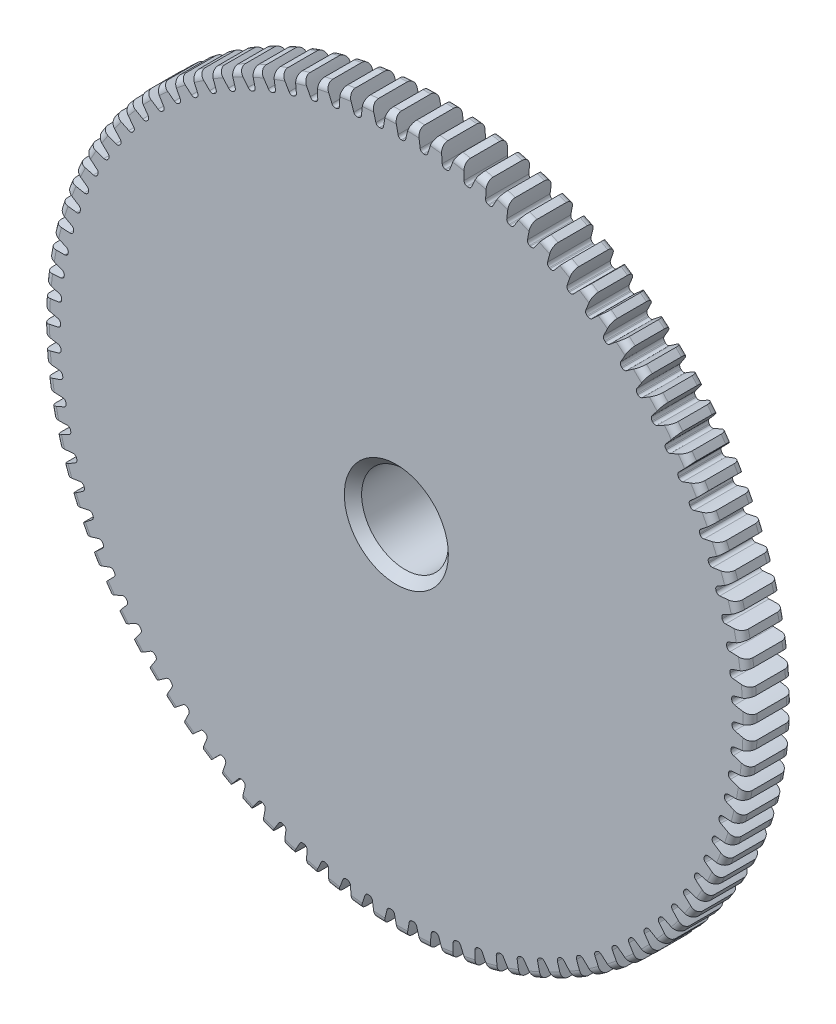
SolidWorks part; units mm, degrees
ref_plane "Front" through (0, 0, 0) normal (0, 0, 1) x (1, 0, 0)
ref_plane "Top" through (0, 0, 0) normal (0, 1, 0) x (1, 0, 0)
ref_plane "Right" through (0, 0, 0) normal (1, 0, 0) x (0, 0, -1)
sketch "Sketch1" plane through (0, 0, 0) normal (0, 0, 1) x (1, 0, 0)
  line L0 (-1219.2, 0) -> (1219.2, 0) construction
  circle A0 centre (0, 0) radius 25.908
  circle A1 centre (0, 0) radius 25.4 construction
  circle A3 centre (0, 0) radius 24.7174 construction
  dimension "D1" = 1.1906
  dimension "OD" = 51.816
  dimension "Ptich Dia" = 50.8
  dimension "Root Dia" = 49.4348
  dimension "D3" = 0.508
  dimension "Number of Teeth" = 2438.4
extrude "Boss-Extrude1" add sketch "Sketch1" against normal blind 3.175
sketch "Sketch2" plane through (0, 0, 0) normal (1, 0, 0) x (0, 0, -1)
  line L0 (3.175, 0) -> (9.525, 0)
  line L1 (3.175, 0) -> (3.175, 12.7)
  line L2 (3.175, 12.7) -> (9.525, 12.7)
  line L3 (9.525, 12.7) -> (9.525, 0)
  point P5 (9.525, -12.7)
  point P6 (0, -25.908)
  point P7 (3.175, -25.908)
  point P9 (0, 25.908)
  dimension "Face Wd" = 3.175
  dimension "B Hub Dia" = 25.4
  dimension "D O'all Lg." = 9.525
revolve "Revolve1" add sketch "Sketch2" angle 360 about L0
fillet "Fillet2" radius 0.5182 3 edges at (25.908, 0, -3.175) (25.908, 0, 0) (12.7, 0, -3.175)
sketch "Sketch3" plane through (0, 0, 0) normal (0, 0, 1) x (1, 0, 0)
  line L0 (0, 0) -> (0, 25.908) construction
  line L1 (-6.1571, 23.8077) -> (0, 25.4)
  line L2 (-9.5921, 25.4) -> (9.5921, 25.4) construction
  line L3 (-9.2865, 22.9983) -> (9.2865, 27.8017) construction
  line L4 (-6.1571, 23.8077) -> (0, 0) construction
  line L5 (-15.7046, 18.923) -> (0, 0) construction
  line L6 (-15.7046, 18.923) -> (-2.5109, 29.8728) construction
  line L7 (-4.2933, 24.2133) -> (0, 0) construction
  line L8 (-4.2933, 24.2133) -> (0.0901, 24.9905) construction
  arc A0 (-6.1571, 23.8077) -> (-15.7046, 18.923) centre (0, 0) ccw
  circle A1 centre (0, 0) radius 25.4 construction
  circle A2 centre (0, 0) radius 24.591 construction
  arc A3 (-6.1571, 23.8077) -> (-4.2933, 24.2133) centre (0, 0) cw
  circle A4 centre (0, 0) radius 25.908 construction
  point P6 (0, 25.4)
  dimension "D1" = 6.3597
  dimension "Pressure Angle" = 14.5
  dimension "D2" = 10.8114
  dimension "D3" = 17.1457
  dimension "D4" = 1.9079
  dimension "D5" = 4.4518
sketch "Sketch4" plane through (0, 0, 0) normal (0, 0, 1) x (1, 0, 0)
  line L0 (0, 0) -> (0.4155, 25.3932) construction
  line L2 (0, 25.4) -> (0.8311, 25.3864) construction
  line L4 (0.16, 24.5904) -> (0, 0) construction
  line L6 (-15.7046, 18.923) -> (-2.5109, 29.8728) construction
  line L7 (-15.7046, 18.923) -> (-2.5109, 29.8728) construction
  arc A0 (0.6447, 24.5825) -> (0.16, 24.5904) centre (0, 0) ccw
  arc A1 (0, 25.4) -> (0.8311, 25.3864) centre (0, 0) cw construction
  circle A2 centre (0, 0) radius 25.4 construction
  circle A3 centre (0, 0) radius 24.591 construction
  arc A5 (3.4869, 29.7746) -> (-2.5109, 29.8728) centre (0, 0) ccw
  spline S0 degree 2 poles (-2.5109, 29.8728) (-0.2902, 27.536) (0.16, 24.5904) knots 0 0 0 1 1 1
  spline S1 degree 2 poles (3.4869, 29.7746) (1.191, 27.5118) (0.6447, 24.5825) knots 0 0 0 1 1 1
  dimension "D1" = 0.8312
extrude "Cut-Extrude1" cut sketch "Sketch4" against normal through all
fillet "Fillet1" radius 0.2494 2 edges at (0.16, 24.5904, -1.5875) (0.6447, 24.5825, -1.5875)
pattern_circular "CirPattern1" count 96 over 360 about axis through (0, 0, -3.175) along (0, 0, 1) of "Cut-Extrude1", "Fillet1"
sketch "Sketch5" plane through (0, 0, 0) normal (0, 0, 1) x (1, 0, 0)
  circle A0 centre (0, 0) radius 3.175
  circle A1 centre (0, 0) radius 1.5875 construction
  dimension "Bore Min" = 6.35
  dimension "Bore Max" = 3.175
extrude "Cut-Extrude2" cut sketch "Sketch5" against normal through all
chamfer "Chamfer1" distance 0.635 angle 45 3 edges at (12.7, 0, -9.525) (3.175, 0, 0) (3.175, 0, -9.525)
sketch "Pitch Dia" plane through (0, 0, 0) normal (0, 0, 1) x (1, 0, 0)
  circle A0 centre (0, 0) radius 25.4 construction
  circle A1 centre (0, 0) radius 25.4 construction
equation "\"D1@Boss-Extrude1\" = \"Face Wd@Sketch2\""
equation "\"D2@Sketch3\" = \"D1@Sketch3\"*1.7"
equation "\"D3@Sketch3\" = \"D1@Sketch3\"+\"D2@Sketch3\"-.001"
equation "\"D4@Sketch3\" = \"D1@Sketch3\"*.3"
equation "\"D5@Sketch3\" = \"D1@Sketch3\"-\"D4@Sketch3\""
equation "\"D1@Sketch4\" = 1.5708/(\"Number of Teeth@Sketch1\"/\"Ptich Dia@Sketch1\")"
equation "\"D1@Chamfer1\" = \"B Hub Dia@Sketch2\"*.025"
equation "\"D1@CirPattern1\" = \"Number of Teeth@Sketch1\""
equation "\"D1@Fillet1\" = \"D1@Sketch4\"*.3"
equation "\"D1@Fillet2\" = \"OD@Sketch1\"*.01"
equation "\"D1@Sketch1\" = 2.250/(\"Number of Teeth@Sketch1\"/\"Ptich Dia@Sketch1\")"
